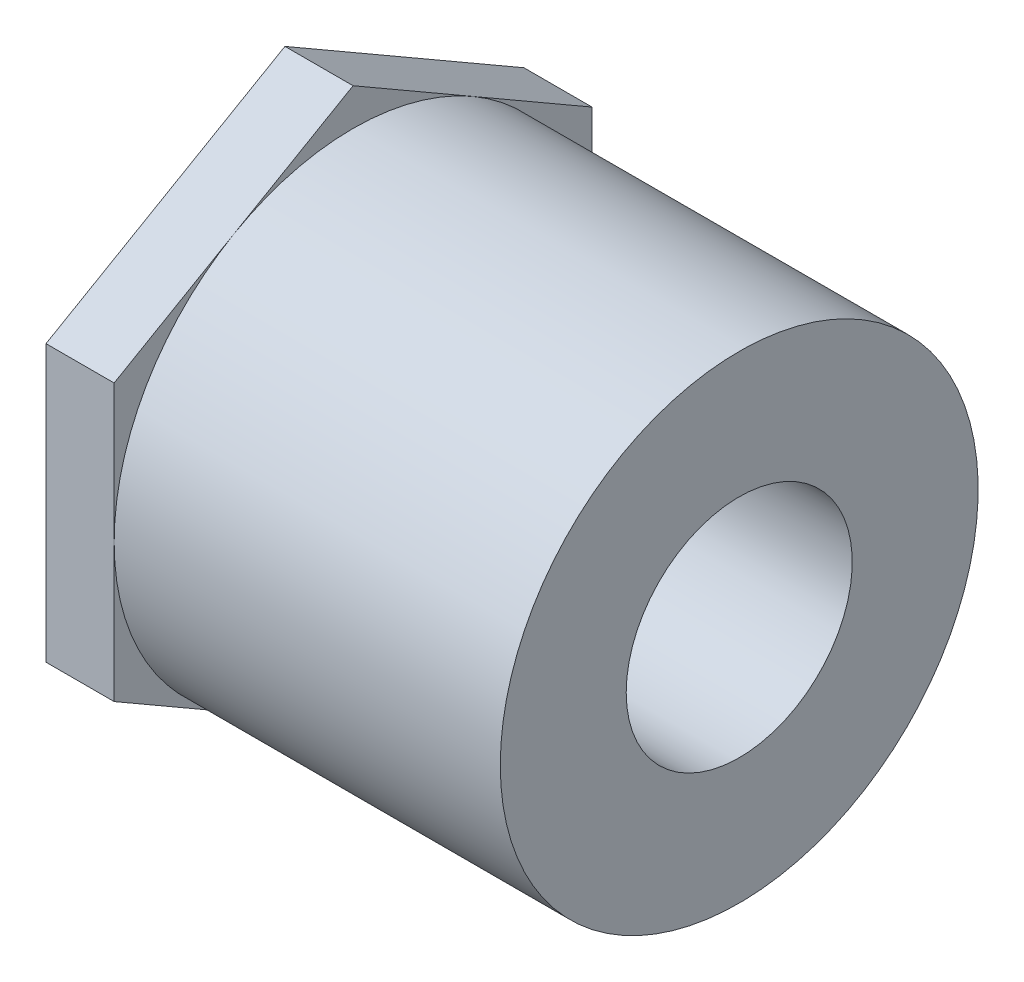
SolidWorks part; units mm, degrees
material "PVC Rigid"
ref_plane "Front Plane" through (0, 0, 0) normal (0, 0, 1) x (1, 0, 0)
ref_plane "Top Plane" through (0, 0, 0) normal (0, 1, 0) x (1, 0, 0)
ref_plane "Right Plane" through (0, 0, 0) normal (1, 0, 0) x (0, 0, -1)
sketch "Sketch0" plane through (0, 0, 0) normal (0, 0, 1) x (1, 0, 0)
  line L0 (-31.75, 0) -> (0, 0) construction
  line L2 (-22.225, 16.7005) -> (-22.225, -16.7005) construction
  line L3 (-26.9875, 16.7005) -> (-26.9875, -16.7005) construction
  line L5 (-11.9062, 10.6172) -> (-31.75, 10.7696) construction
  line L6 (-11.9062, 10.6172) -> (-11.9062, -10.6172) construction
  line L7 (-11.9062, -10.6172) -> (-31.75, -10.7696) construction
  line L8 (-31.75, 10.7696) -> (-31.75, -10.7696) construction
  line L14 (-11.9062, 7.8994) -> (-11.9062, -7.8994) construction
  line L21 (-31.75, 0) -> (-11.9062, 0) construction
  point P12 (-22.225, 0)
  point P27 (-26.9875, 0)
  dimension "A" = 31.75
  dimension "OD A 2" = 21.5392
  dimension "OD B 2" = 21.2344
  dimension "ID 2" = 15.7988
  dimension "B" = 11.9062
  dimension "Pipe OD 1" = 33.401
  dimension "C 1" = 22.225
  dimension "J" = 33.401
  dimension "K" = 4.7625
sketch "Sketch1" plane through (0, 0, 0) normal (0, 0, 1) x (1, 0, 0)
  line L0 (-31.75, 0) -> (0, 0) construction
  line L1 (-31.75, 0) -> (0, 0) construction
  line L2 (-31.75, -16.7005) -> (0, -16.7005)
  line L3 (0, -7.8994) -> (0, -16.7005)
  line L4 (-31.75, -16.7005) -> (-31.75, -10.7696)
  line L5 (-31.75, -10.7696) -> (-11.9062, -10.6172)
  line L6 (0, 0) -> (0, -7.8994) construction
  line L8 (-11.9062, -7.8994) -> (-11.9062, -10.6172)
  line L11 (-11.9062, -7.8994) -> (0, -7.8994)
revolve "Revolve1" add sketch "Sketch1" angle 360 about L1
sketch "Sketch2" plane through (-31.75, 0, 0) normal (-1, 0, 0) x (0, 0, 1)
  line L0 (0, 0) -> (0, 19.2841) construction
  line L1 (0, 19.2841) -> (-16.7005, 9.642)
  line L2 (-16.7005, 9.642) -> (-16.7005, -9.642)
  line L3 (-16.7005, -9.642) -> (0, -19.2841)
  line L4 (0, -19.2841) -> (16.7005, -9.642)
  line L5 (16.7005, -9.642) -> (16.7005, 9.642)
  line L6 (16.7005, 9.642) -> (0, 19.2841)
  circle A0 centre (0, 0) radius 10.7696 construction
  circle A1 centre (0, 0) radius 10.7696
  circle A2 centre (0, 0) radius 16.7005 construction
  point P3 (0, 16.7005)
extrude "Boss-Extrude1" add sketch "Sketch2" against normal up to vertex (4.7625 mm away) up to point (-26.9875, 0, 0)
